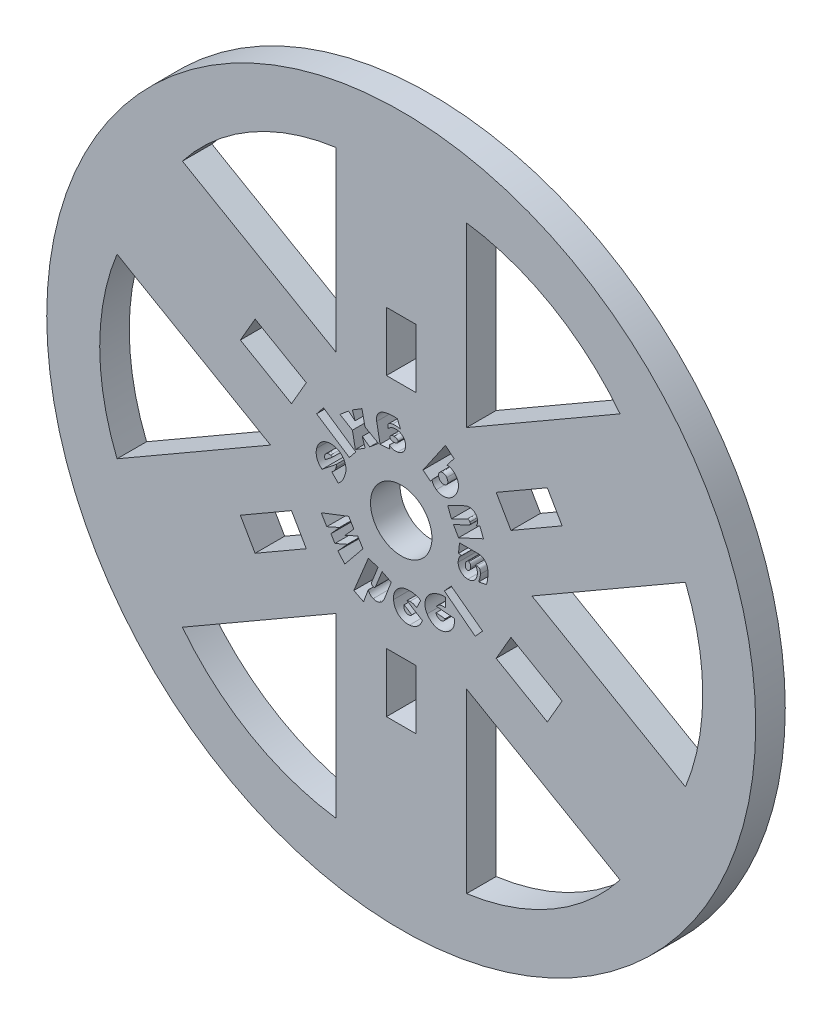
SolidWorks part; units mm, degrees
ref_plane "Front Plane" through (0, 0, 0) normal (0, 0, 1) x (1, 0, 0)
ref_plane "Top Plane" through (0, 0, 0) normal (0, 1, 0) x (1, 0, 0)
ref_plane "Right Plane" through (0, 0, 0) normal (1, 0, 0) x (0, 0, -1)
sketch "Sketch1" plane through (0, 0, 0) normal (0, 0, 1) x (1, 0, 0)
  circle A0 centre (0, 0) radius 38.1
  dimension "D1" = 76.2
extrude "Extrude1" add sketch "Sketch1" along normal blind 3.175
sketch "Sketch2" plane through (0, 0, 3.175) normal (0, 0, 1) x (1, 0, 0)
  circle A0 centre (0, 0) radius 3.302
extrude "Cut-Extrude1" cut sketch "Sketch2" against normal through all
sketch "Sketch3" plane through (0, 0, 3.175) normal (0, 0, 1) x (1, 0, 0)
  line L0 (0, 38.1) -> (0, -38.1) construction
  line L1 (-32.9956, 19.05) -> (32.9956, -19.05) construction
  line L2 (-32.9956, -19.05) -> (32.9956, 19.05) construction
  line L3 (-17.2915, 8.1502) -> (-15.704, 10.8998)
  line L4 (-15.704, 10.8998) -> (-10.2048, 7.7248)
  line L5 (-10.2048, 7.7248) -> (-11.7923, 4.9752)
  line L6 (-17.2915, 8.1502) -> (-11.7923, 4.9752)
  line L7 (-1.5875, 19.05) -> (-1.5875, 12.7)
  line L8 (-1.5875, 19.05) -> (1.5875, 19.05)
  line L9 (1.5875, 19.05) -> (1.5875, 12.7)
  line L10 (1.5875, 12.7) -> (-1.5875, 12.7)
  line L11 (15.704, 10.8998) -> (10.2048, 7.7248)
  line L12 (15.704, 10.8998) -> (17.2915, 8.1502)
  line L13 (17.2915, 8.1502) -> (11.7923, 4.9752)
  line L14 (11.7923, 4.9752) -> (10.2048, 7.7248)
  line L15 (17.2915, -8.1502) -> (11.7923, -4.9752)
  line L16 (17.2915, -8.1502) -> (15.704, -10.8998)
  line L17 (15.704, -10.8998) -> (10.2048, -7.7248)
  line L18 (10.2048, -7.7248) -> (11.7923, -4.9752)
  line L19 (1.5875, -19.05) -> (1.5875, -12.7)
  line L20 (1.5875, -19.05) -> (-1.5875, -19.05)
  line L21 (-1.5875, -19.05) -> (-1.5875, -12.7)
  line L22 (-1.5875, -12.7) -> (1.5875, -12.7)
  line L23 (-15.704, -10.8998) -> (-10.2048, -7.7248)
  line L24 (-15.704, -10.8998) -> (-17.2915, -8.1502)
  line L25 (-17.2915, -8.1502) -> (-11.7923, -4.9752)
  line L26 (-11.7923, -4.9752) -> (-10.2048, -7.7248)
  circle A0 centre (0, 0) radius 38.1 construction
  circle A2 centre (0, 0) radius 25.4 construction
  circle A3 centre (-25.4, 0) radius 12.7 construction
  point P19 (-10.9985, 6.35)
  point P20 (-16.4978, 9.525)
  dimension "D1" = 60
  dimension "D3" = 50.8
  dimension "D4" = 6.35
  dimension "D2" = 60
  dimension "D5" = 1.5875
  dimension "D6" = 19.05
extrude "Cut-Extrude2" cut sketch "Sketch3" against normal through all contours L10 L9 L8 L7 | L3 L6 L5 L4 | L26 L25 L24 L23 | L22 L21 L20 L19 | L18 L17 L16 L15 | L14 L13 L12 L11
sketch "Sketch4" plane through (0, 0, 3.175) normal (0, 0, 1) x (1, 0, 0)
  line L0 (0, 0) -> (0, 47.4998) construction
  line L1 (0, 0) -> (25, 43.3013) construction
  line L2 (7.0231, 12.1643) -> (7.0231, 31.2143)
  line L3 (7.0231, 12.1643) -> (23.5209, 21.6893)
  line L4 (14.0462, 0) -> (30.544, 9.525)
  line L5 (14.0462, 0) -> (30.544, -9.525)
  line L6 (7.0231, -12.1643) -> (23.5209, -21.6893)
  line L7 (7.0231, -12.1643) -> (7.0231, -31.2143)
  line L8 (-7.0231, -12.1643) -> (-7.0231, -31.2143)
  line L9 (-7.0231, -12.1643) -> (-23.5209, -21.6893)
  line L10 (-14.0462, 0) -> (-30.544, -9.525)
  line L11 (-14.0462, 0) -> (-30.544, 9.525)
  line L12 (-7.0231, 12.1643) -> (-23.5209, 21.6893)
  line L13 (-7.0231, 12.1643) -> (-7.0231, 31.2143)
  circle A1 centre (0, 0) radius 14.0462 construction
  arc A2 (7.0231, 31.2143) -> (23.5209, 21.6893) centre (3.5534, 6.1546) cw
  arc A3 (30.544, 9.525) -> (30.544, -9.525) centre (7.1067, 0) cw
  arc A4 (23.5209, -21.6893) -> (7.0231, -31.2143) centre (3.5534, -6.1546) cw
  arc A5 (-7.0231, -31.2143) -> (-23.5209, -21.6893) centre (-3.5534, -6.1546) cw
  arc A6 (-30.544, -9.525) -> (-30.544, 9.525) centre (-7.1067, 0) cw
  arc A7 (-23.5209, 21.6893) -> (-7.0231, 31.2143) centre (-3.5534, 6.1546) cw
  dimension "D2" = 19.05
  dimension "D3" = 19.05
  dimension "D1" = 30
  dimension "D4" = 60
extrude "Cut-Extrude3" cut sketch "Sketch4" against normal through all
sketch "Sketch5" plane through (0, 0, 0) normal (0, 0, -1) x (-1, 0, 0)
  circle A0 centre (0, 0) radius 6.35 construction
  text T0 "wheel and axle" font "GROBOLD" height in points 17
extrude "Cut-Extrude4" cut sketch "Sketch5" against normal through all
